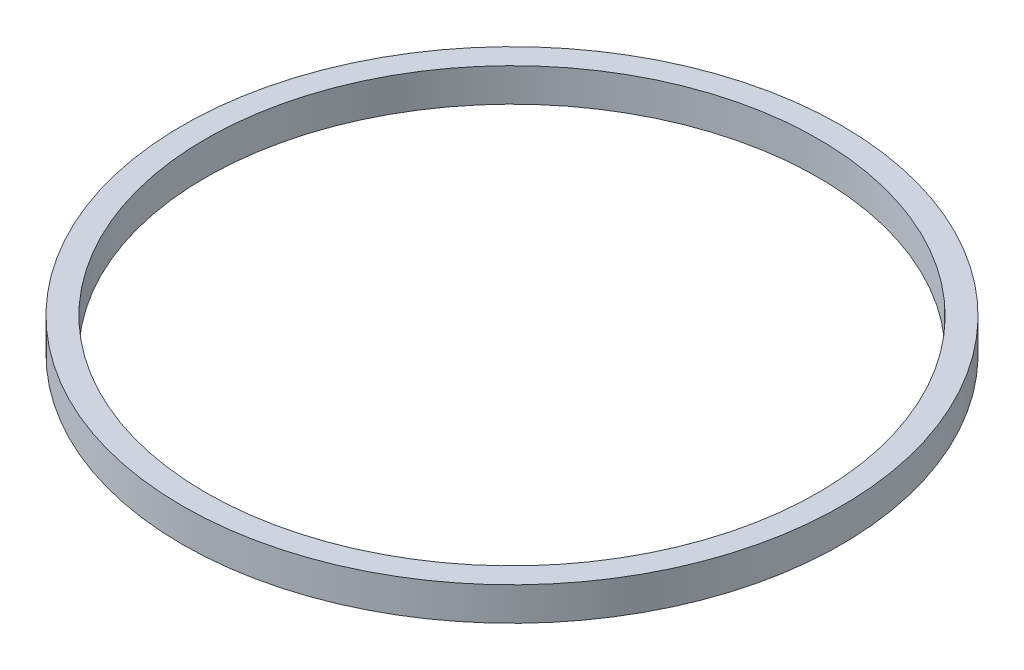
SolidWorks part; units mm, degrees
ref_plane "Front Plane" through (0, 0, 0) normal (0, 0, 1) x (1, 0, 0)
ref_plane "Top Plane" through (0, 0, 0) normal (0, 1, 0) x (1, 0, 0)
ref_plane "Right Plane" through (0, 0, 0) normal (1, 0, 0) x (0, 0, -1)
sketch "Sketch3" plane through (0, 0, 0) normal (0, 1, 0) x (1, 0, 0)
  circle A0 centre (0, 0) radius 1003.3
  circle A1 centre (0, 0) radius 1079.5
  dimension "D1" = 2159
  dimension "D2" = 2006.6
extrude "Boss-Extrude2" add sketch "Sketch3" along normal blind 109.22
